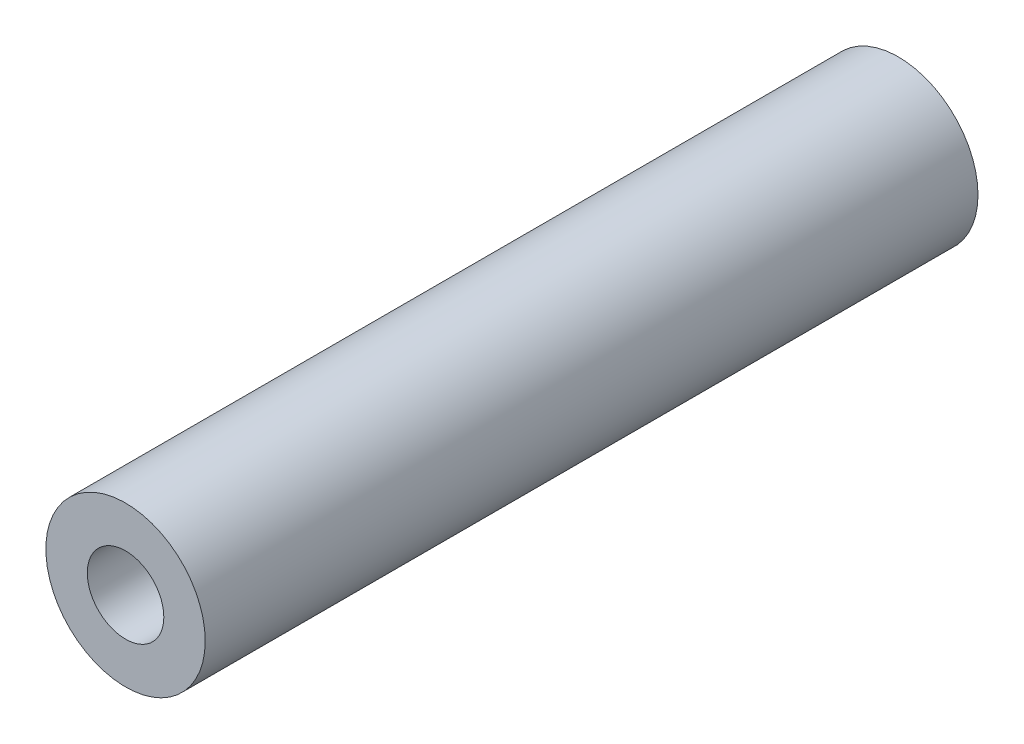
SolidWorks part; units mm, degrees
material "AISI 316 Stainless Steel Sheet (SS)"
ref_plane "Front Plane" through (0, 0, 0) normal (0, 0, 1) x (1, 0, 0)
ref_plane "Top Plane" through (0, 0, 0) normal (0, 1, 0) x (1, 0, 0)
ref_plane "Right Plane" through (0, 0, 0) normal (1, 0, 0) x (0, 0, -1)
sketch "Sketch1" plane through (0, 0, 0) normal (0, 0, 1) x (1, 0, 0)
  circle A0 centre (-7.7242, 4.7099) radius 0.2578
  dimension "D1" = 0.5156
extrude "Extrude1" add sketch "Sketch1" along normal blind 2.5
sketch "Sketch2" plane through (0, 0, 2.5) normal (0, 0, 1) x (1, 0, 0)
  circle A0 centre (-7.7242, 4.7099) radius 0.1238
  circle A1 centre (-7.7242, 4.7099) radius 0.2578 construction
  dimension "D1" = 0.2476
  dimension "D2" = 0.134
extrude "Cut-Extrude1" cut sketch "Sketch2" against normal blind 2.5
